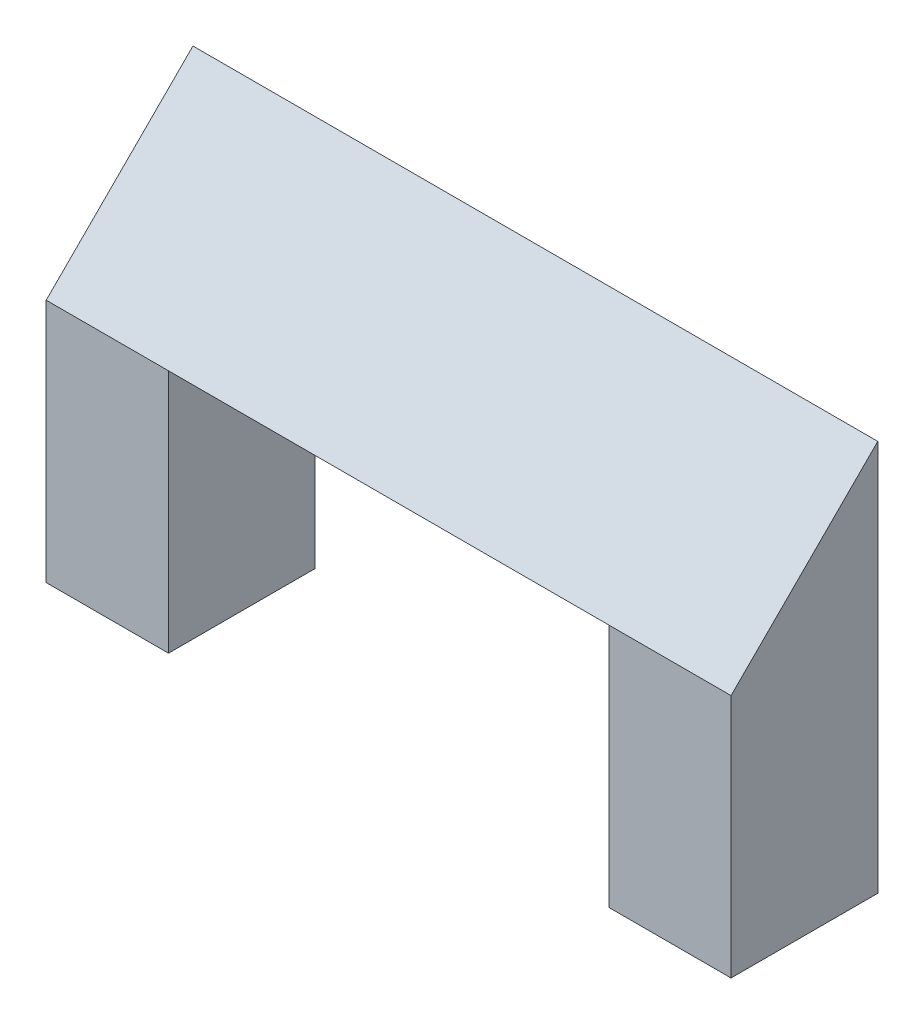
SolidWorks part; units mm, degrees
ref_plane "Front Plane" through (0, 0, 0) normal (0, 0, 1) x (1, 0, 0)
ref_plane "Top Plane" through (0, 0, 0) normal (0, 1, 0) x (1, 0, 0)
ref_plane "Right Plane" through (0, 0, 0) normal (1, 0, 0) x (0, 0, -1)
sketch "Sketch1" plane through (0, 0, 0) normal (0, 1, 0) x (1, 0, 0)
  line L5 (-43.5321, 17.3394) -> (-18.5321, 17.3394)
  line L6 (-43.5321, 17.3394) -> (-43.5321, -12.6606)
  line L7 (-43.5321, -12.6606) -> (-18.5321, -12.6606)
  line L8 (-18.5321, 17.3394) -> (-18.5321, -12.6606)
  line L9 (71.4679, 17.3394) -> (96.4679, 17.3394)
  line L10 (71.4679, 17.3394) -> (71.4679, -12.6606)
  line L11 (71.4679, -12.6606) -> (96.4679, -12.6606)
  line L12 (96.4679, 17.3394) -> (96.4679, -12.6606)
  dimension "D1" = 30
  dimension "D2" = 30
  dimension "D3" = 140
  dimension "D4" = 90
  dimension "D5" = 25
extrude "Boss-Extrude1" add sketch "Sketch1" along normal blind 50
sketch "Sketch2" plane through (96.4679, 0, 0) normal (1, 0, 0) x (0, 0, -1)
  line L0 (-12.6606, 50) -> (17.3394, 50)
  line L1 (17.3394, 50) -> (17.3394, 80)
  line L2 (17.3394, 80) -> (-12.6606, 50)
  dimension "D1" = 45
extrude "Boss-Extrude2" add sketch "Sketch2" against normal up to vertex
sketch "Sketch3" plane through (-18.5321, 0, 0) normal (1, 0, 0) x (0, 0, -1)
  line L0 (-12.6606, 50) -> (17.3394, 39.0809)
  line L1 (17.3394, 0) -> (17.3394, 80) construction
  line L2 (17.3394, 39.0809) -> (17.3394, 50)
  line L3 (17.3394, 50) -> (-12.6606, 50)
  dimension "D1" = 20
extrude "Boss-Extrude3" add sketch "Sketch3" along normal up to vertex (90 mm away)
